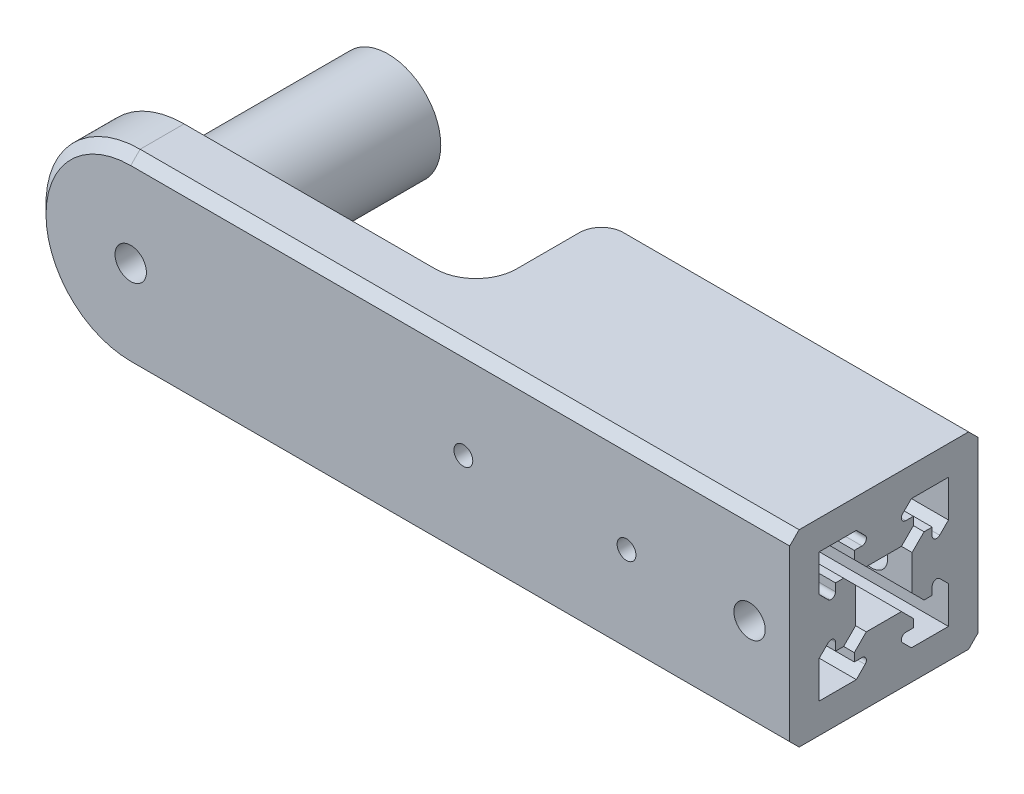
SolidWorks part; units mm, degrees
ref_plane "Front Plane" through (0, 0, 0) normal (0, 0, 1) x (1, 0, 0)
ref_plane "Top Plane" through (0, 0, 0) normal (0, 1, 0) x (1, 0, 0)
ref_plane "Right Plane" through (0, 0, 0) normal (1, 0, 0) x (0, 0, -1)
sketch "Sketch1" plane through (0, 0, 0) normal (0, 0, 1) x (1, 0, 0)
  circle A0 centre (0, 0) radius 8.4
  dimension "D1" = 16.8
extrude "Boss-Extrude1" add sketch "Sketch1" along normal blind 30
sketch "Sketch3" plane through (0, 0, 30) normal (0, 0, 1) x (1, 0, 0)
  circle A0 centre (0, 0) radius 10
  dimension "D1" = 20
extrude "Boss-Extrude2" add sketch "Sketch3" along normal blind 1
sketch "Sketch4" plane through (0, 0, 31) normal (0, 0, 1) x (1, 0, 0)
  line L0 (0, 15) -> (105, 15)
  line L1 (105, 15) -> (105, -15)
  line L2 (105, -15) -> (0, -15)
  arc A0 (0, 15) -> (0, -15) centre (0, 0) ccw
  dimension "D1" = 30
  dimension "D2" = 105
extrude "Boss-Extrude3" add sketch "Sketch4" along normal blind 10
sketch "Sketch5" plane through (0, 15, 0) normal (0, 1, 0) x (1, 0, 0)
  line L0 (40, -31) -> (105, -31)
  line L2 (105, -31) -> (105, -11)
  line L3 (105, -11) -> (50, -11)
  line L4 (45, -26) -> (45, -16)
  arc A0 (40, -31) -> (45, -26) centre (40, -26) ccw
  arc A1 (50, -11) -> (45, -16) centre (50, -16) ccw
  point P11 (45, -11)
  dimension "D3" = 5
  dimension "D4" = 5
  dimension "D1" = 60
  dimension "D2" = 20
extrude "Boss-Extrude4" add sketch "Sketch5" against normal blind 30
sketch "Sketch6" plane through (105, 0, 0) normal (1, 0, 0) x (0, 0, -1)
  line L0 (-23.1971, 4.5537) -> (-28.8029, 4.5537)
  line L1 (-28.8029, 4.5537) -> (-30.7101, 6.4608)
  line L2 (-30.7101, 6.4608) -> (-30.7101, 7.7537)
  line L3 (-30.7101, 7.7537) -> (-29.4828, 7.7537)
  line L4 (-28.9879, 8.9487) -> (-30.3879, 10.3487)
  line L5 (-36.295, 4.4416) -> (-34.895, 3.0416)
  line L6 (-33.7, 3.5366) -> (-33.7, 4.7638)
  line L7 (-33.7, 4.7638) -> (-32.4071, 4.7638)
  line L8 (-32.4071, 4.7638) -> (-30.5, 2.8567)
  line L9 (-30.5, 2.8567) -> (-30.5, -2.7492)
  line L10 (-30.5, -2.7492) -> (-32.4071, -4.6563)
  line L11 (-32.4071, -4.6563) -> (-33.7, -4.6563)
  line L12 (-33.7, -4.6563) -> (-33.7, -3.4291)
  line L13 (-34.895, -2.9342) -> (-36.295, -4.3342)
  line L14 (-30.3879, -10.2413) -> (-28.9879, -8.8413)
  line L15 (-29.4828, -7.6463) -> (-30.7101, -7.6463)
  line L16 (-30.7101, -7.6463) -> (-30.7101, -6.3534)
  line L17 (-30.7101, -6.3534) -> (-28.8029, -4.4463)
  line L18 (-28.8029, -4.4463) -> (-23.1971, -4.4463)
  line L19 (-30.3879, -10.2413) -> (-36.295, -10.2413)
  line L20 (-36.295, -10.2413) -> (-36.295, -4.3342)
  line L21 (-36.295, 4.4416) -> (-36.295, 10.3487)
  line L22 (-36.295, 10.3487) -> (-30.3879, 10.3487)
  line L23 (-26, 15.3277) -> (-26, -14.6723) construction
  line L24 (-15.705, 10.3487) -> (-21.6121, 10.3487)
  line L25 (-15.705, 4.4416) -> (-15.705, 10.3487)
  line L26 (-15.705, -10.2413) -> (-15.705, -4.3342)
  line L27 (-21.6121, -10.2413) -> (-15.705, -10.2413)
  line L28 (-21.2899, -6.3534) -> (-23.1971, -4.4463)
  line L29 (-21.2899, -7.6463) -> (-21.2899, -6.3534)
  line L30 (-22.5172, -7.6463) -> (-21.2899, -7.6463)
  line L31 (-21.6121, -10.2413) -> (-23.0121, -8.8413)
  line L32 (-17.105, -2.9342) -> (-15.705, -4.3342)
  line L33 (-18.3, -4.6563) -> (-18.3, -3.4291)
  line L34 (-19.5929, -4.6563) -> (-18.3, -4.6563)
  line L35 (-21.5, -2.7492) -> (-19.5929, -4.6563)
  line L36 (-21.5, 2.8567) -> (-21.5, -2.7492)
  line L37 (-19.5929, 4.7638) -> (-21.5, 2.8567)
  line L38 (-18.3, 4.7638) -> (-19.5929, 4.7638)
  line L39 (-18.3, 3.5366) -> (-18.3, 4.7638)
  line L40 (-15.705, 4.4416) -> (-17.105, 3.0416)
  line L41 (-23.0121, 8.9487) -> (-21.6121, 10.3487)
  line L42 (-21.2899, 7.7537) -> (-22.5172, 7.7537)
  line L43 (-21.2899, 6.4608) -> (-21.2899, 7.7537)
  line L44 (-23.1971, 4.5537) -> (-21.2899, 6.4608)
  line L45 (-41, 15) -> (-11, 15) construction
  arc A0 (-23.0121, -8.8413) -> (-22.5172, -7.6463) centre (-22.5172, -8.3463) cw
  arc A1 (-29.4828, 7.7537) -> (-28.9879, 8.9487) centre (-29.4828, 8.4537) ccw
  arc A2 (-18.3, -3.4291) -> (-17.105, -2.9342) centre (-17.6, -3.4291) cw
  arc A3 (-17.105, 3.0416) -> (-18.3, 3.5366) centre (-17.6, 3.5366) cw
  arc A4 (-34.895, 3.0416) -> (-33.7, 3.5366) centre (-34.4, 3.5366) ccw
  arc A5 (-33.7, -3.4291) -> (-34.895, -2.9342) centre (-34.4, -3.4291) ccw
  arc A6 (-22.5172, 7.7537) -> (-23.0121, 8.9487) centre (-22.5172, 8.4537) cw
  arc A7 (-28.9879, -8.8413) -> (-29.4828, -7.6463) centre (-29.4828, -8.3463) ccw
  point P66 (-26, 15)
  dimension "D7" = 0.7
  dimension "D16" = 0.7
  dimension "D31" = 0.7
  dimension "D1" = 5.6059
  dimension "D2" = 2.6971
  dimension "D3" = 1.2929
  dimension "D4" = 2.595
  dimension "D5" = 135
  dimension "D6" = 1.2934
  dimension "D8" = 1.9799
  dimension "D9" = 135
  dimension "D10" = 1.2272
  dimension "D11" = 5.6059
  dimension "D12" = 2.6971
  dimension "D13" = 1.2929
  dimension "D14" = 1.2272
  dimension "D15" = 1.2934
  dimension "D17" = 1.9799
  dimension "D18" = 225
  dimension "D19" = 5.9071
  dimension "D20" = 135
  dimension "D21" = 90
  dimension "D22" = 135
  dimension "D23" = 2.595
  dimension "D24" = 135
  dimension "D25" = 135
  dimension "D26" = 1.2934
  dimension "D27" = 5.9071
  dimension "D28" = 1.9799
  dimension "D29" = 135
  dimension "D30" = 1.2934
  dimension "D32" = 1.2272
  dimension "D33" = 90
  dimension "D34" = 135
  dimension "D35" = 1.2929
  dimension "D36" = 2.595
  dimension "D37" = 2.6971
  dimension "D38" = 5.6059
  dimension "D39" = 5.9071
extrude "Cut-Extrude1" cut sketch "Sketch6" against normal blind 66
chamfer "Chamfer1" distance 1.5 angle 45 14 edges at (77.5, 15, 11) (77.5, -15, 11) (46.4645, 15, 12.4645) (46.4645, -15, 12.4645) (45, -15, 21) (45, 15, 21) (43.5355, -15, 29.5355) (43.5355, 15, 29.5355) (20, -15, 31) (-15, 0, 31) (20, 15, 31) (52.5, -15, 41) (-15, 0, 41) (52.5, 15, 41)
sketch "Sketch7" plane through (0, 0, 41) normal (0, 0, 1) x (1, 0, 0)
  line L0 (105, -13.5) -> (105, 13.5) construction
  circle A0 centre (53, 0) radius 1.5
  circle A1 centre (79, 0) radius 1.5
  circle A2 centre (98.6, 0) radius 2.5
  circle A3 centre (0, 0) radius 2.5
  dimension "D4" = 5
  dimension "D5" = 3
  dimension "D6" = 5
  dimension "D7" = 3
  dimension "D1" = 52
  dimension "D2" = 26
  dimension "D3" = 19.6
extrude "Cut-Extrude2" cut sketch "Sketch7" against normal through all
